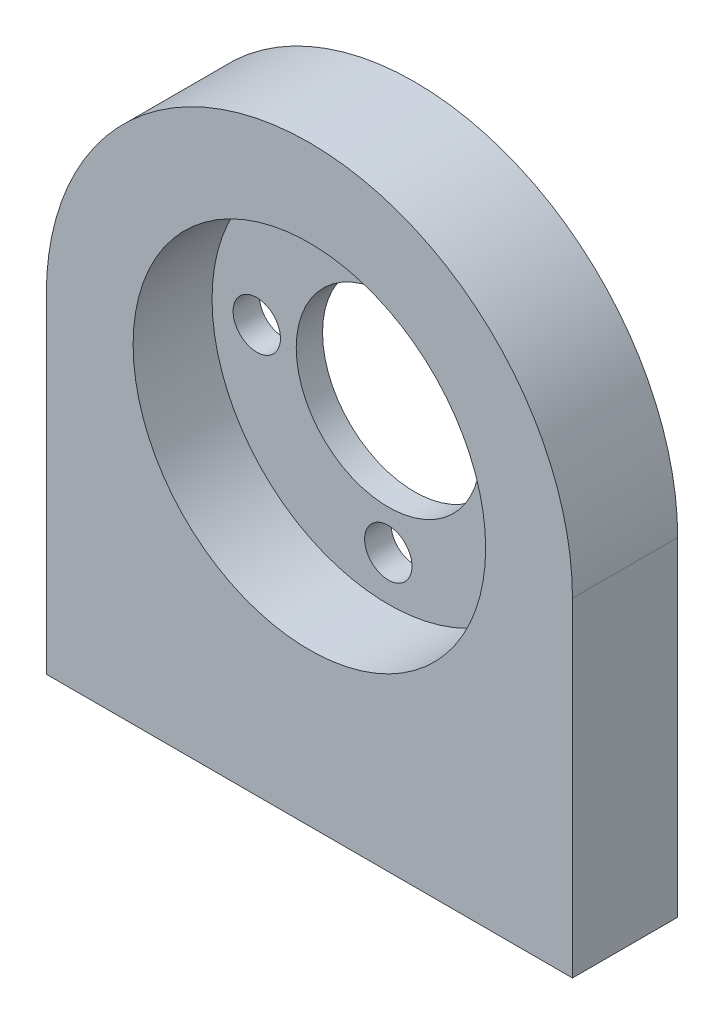
SolidWorks part; units mm, degrees
ref_plane "Plan de face" through (0, 0, 0) normal (0, 0, 1) x (1, 0, 0)
ref_plane "Plan de dessus" through (0, 0, 0) normal (0, 1, 0) x (1, 0, 0)
ref_plane "Plan de droite" through (0, 0, 0) normal (1, 0, 0) x (0, 0, -1)
sketch "Esquisse1" plane through (0, 0, 0) normal (0, 0, 1) x (1, 0, 0)
  line L0 (0, 0) -> (0, 10) construction
  line L1 (-20, 0) -> (20, 0) construction
  line L2 (-20, 0) -> (-20, -25)
  line L3 (-20, -25) -> (20, -25)
  line L4 (20, 0) -> (20, -25)
  circle A0 centre (0, 0) radius 20 construction
  arc A1 (-20, 0) -> (20, 0) centre (0, 0) cw
  circle A2 centre (0, 0) radius 7
  circle A3 centre (0, 10) radius 1.8
  circle A4 centre (10, 0) radius 1.8
  circle A5 centre (0, -10) radius 1.8
  circle A6 centre (-10, 0) radius 1.8
  point P20 (0, 0)
  dimension "D3" = 14
  dimension "D5" = 3.6
  dimension "D1" = 40
  dimension "D2" = 25
  dimension "D4" = 10
  dimension "D6" = 4
extrude "Boss.-Extru.1" add sketch "Esquisse1" along normal blind 8
sketch "Esquisse2" plane through (0, 0, 8) normal (0, 0, 1) x (1, 0, 0)
  circle A0 centre (0, 0) radius 13.4
  dimension "D1" = 26.8
extrude "Enlèv. mat.-Extru.1" cut sketch "Esquisse2" against normal blind 6
sketch "Esquisse3" plane through (0, -25, 0) normal (0, -1, 0) x (1, 0, 0)
  line L0 (-15, 4) -> (15, 4) construction
  line L1 (0, 0) -> (0, 8) construction
  line L2 (-20, 8) -> (20, 8) construction
  line L3 (-20, 8) -> (-20, 0) construction
  circle A0 centre (-15, 4) radius 2
  circle A1 centre (15, 4) radius 2
  point P8 (0, 4)
  point P9 (0, 4)
  dimension "D1" = 4
  dimension "D2" = 5
extrude "Enlèv. mat.-Extru.2" cut sketch "Esquisse3" against normal blind 12
chamfer "Chanfrein1" distance 1 angle 45 2 edges at (15, -25, 2) (-15, -25, 2)
